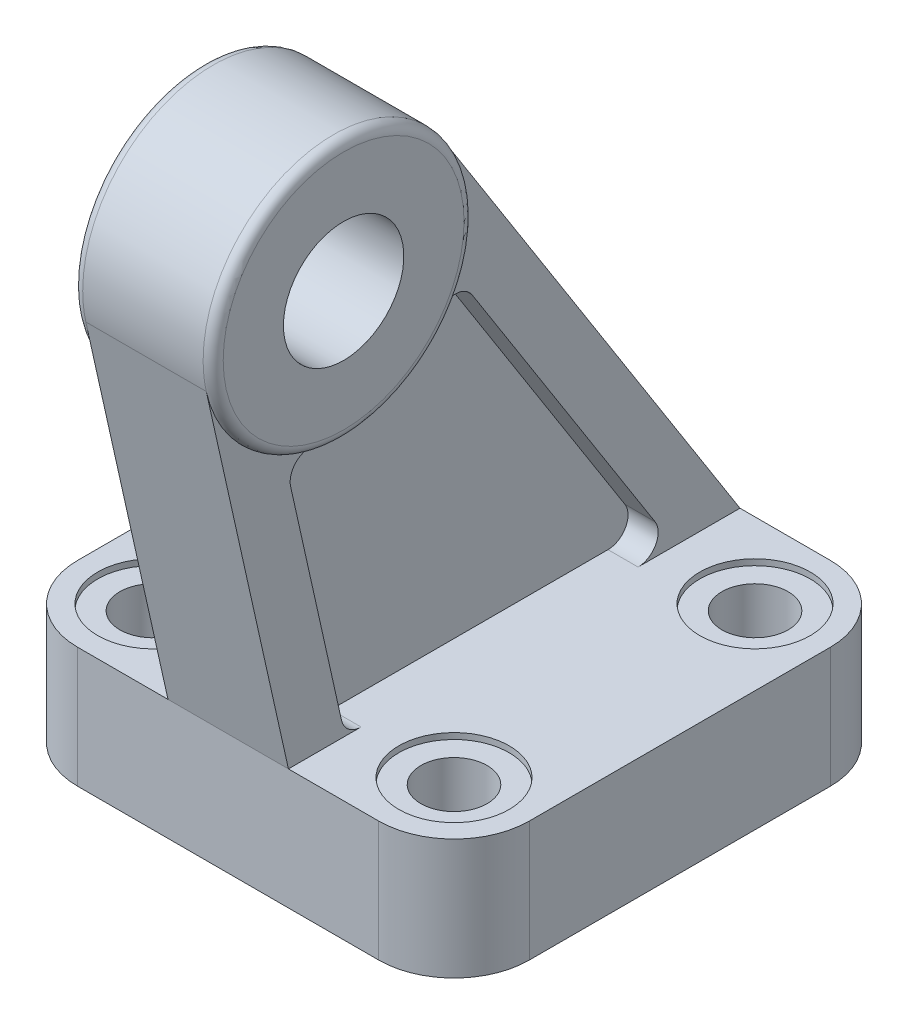
SolidWorks part; units mm, degrees
ref_plane "Front Plane" through (0, 0, 0) normal (0, 0, 1) x (1, 0, 0)
ref_plane "Top Plane" through (0, 0, 0) normal (0, 1, 0) x (1, 0, 0)
ref_plane "Right Plane" through (0, 0, 0) normal (1, 0, 0) x (0, 0, -1)
ref_plane "Plane1" through (0, 0, 0) normal (0, 1, 0) x (1, 0, 0)
sketch "Sketch1" plane through (0, 0, 0) normal (0, 1, 0) x (1, 0, 0)
  line L0 (-15, -22.5) -> (15, -22.5)
  line L1 (22.5, -15) -> (22.5, 15)
  line L2 (15, 22.5) -> (-15, 22.5)
  line L3 (-22.5, 15) -> (-22.5, -15)
  arc A0 (-22.5, -15) -> (-15, -22.5) centre (-15, -15) ccw
  arc A1 (15, -22.5) -> (22.5, -15) centre (15, -15) ccw
  arc A2 (22.5, 15) -> (15, 22.5) centre (15, 15) ccw
  arc A3 (-15, 22.5) -> (-22.5, 15) centre (-15, 15) ccw
  circle A4 centre (15, 15) radius 3.3
  circle A5 centre (15, -15) radius 3.3
  circle A6 centre (-15, 15) radius 3.3
  circle A7 centre (-15, -15) radius 3.3
extrude "Boss-Extrude1" add sketch "Sketch1" along normal blind 12
ref_plane "Plane2" through (0, 0, 0) normal (1, 0, 0) x (0, 0, -1)
sketch "Sketch2" plane through (0, 0, 0) normal (1, 0, 0) x (0, 0, -1)
  line L0 (-30.6875, 48.6669) -> (-22.5, 12)
  line L1 (-22.5, 12) -> (22.5, 12)
  line L2 (22.5, 12) -> (-7.0275, 58.4718)
  arc A0 (-7.0275, 58.4718) -> (-30.6875, 48.6669) centre (-18, 51.5) cw
extrude "Boss-Extrude2" add sketch "Sketch2" against normal blind 6 and the other way blind 6
ref_plane "Plane3" through (6, 0, 0) normal (1, 0, 0) x (0, 0, -1)
sketch "Sketch3" plane through (6, 0, 0) normal (1, 0, 0) x (0, 0, -1)
  line L0 (-22.2785, 36.2457) -> (-17.2138, 13.5641)
  line L1 (-15.2619, 12) -> (12.3433, 12)
  line L2 (14.0314, 15.0726) -> (-4.1857, 43.7434)
  arc A0 (-20.0164, 38.6573) -> (-22.2785, 36.2457) centre (-20.3266, 36.6815) ccw
  arc A1 (-17.2138, 13.5641) -> (-15.2619, 12) centre (-15.2619, 14) ccw
  arc A2 (12.3433, 12) -> (14.0314, 15.0726) centre (12.3433, 14) ccw
  arc A3 (-4.1857, 43.7434) -> (-7.4906, 43.8481) centre (-5.8737, 42.6708) ccw
  arc A4 (-7.4906, 43.8481) -> (-20.0164, 38.6573) centre (-18, 51.5) cw
extrude "Cut-Extrude1" cut sketch "Sketch3" against normal blind 3
ref_plane "Plane4" through (-6, 0, 0) normal (1, 0, 0) x (0, 0, -1)
sketch "Sketch4" plane through (-6, 0, 0) normal (1, 0, 0) x (0, 0, -1)
  line L0 (-22.2785, 36.2457) -> (-17.2138, 13.5641)
  line L1 (-15.2619, 12) -> (12.3433, 12)
  line L2 (14.0314, 15.0726) -> (-4.1857, 43.7434)
  arc A0 (-20.0164, 38.6573) -> (-22.2785, 36.2457) centre (-20.3266, 36.6815) ccw
  arc A1 (-17.2138, 13.5641) -> (-15.2619, 12) centre (-15.2619, 14) ccw
  arc A2 (12.3433, 12) -> (14.0314, 15.0726) centre (12.3433, 14) ccw
  arc A3 (-4.1857, 43.7434) -> (-7.4906, 43.8481) centre (-5.8737, 42.6708) ccw
  arc A4 (-7.4906, 43.8481) -> (-20.0164, 38.6573) centre (-18, 51.5) cw
extrude "Cut-Extrude2" cut sketch "Sketch4" along normal blind 3
ref_plane "Plane5" through (0, 0, 18) normal (0, 0, 1) x (1, 0, 0)
sketch "Sketch5" plane through (0, 0, 18) normal (0, 0, 1) x (1, 0, 0)
  line L0 (-7, 63.5) -> (-7, 57.5)
  line L1 (-7, 57.5) -> (7, 57.5)
  line L2 (7, 57.5) -> (7, 63.5)
  line L3 (6, 64.5) -> (-6, 64.5)
  line L4 (7, 51.5) -> (-7, 51.5) construction
  arc A0 (7, 63.5) -> (6, 64.5) centre (6, 63.5) ccw
  arc A1 (-6, 64.5) -> (-7, 63.5) centre (-6, 63.5) ccw
revolve "Revolve1" add sketch "Sketch5" angle 360 about L4
ref_plane "Plane6" through (0, 0, 0) normal (0, 1, 0) x (1, 0, 0)
sketch "Sketch6" plane through (0, 0, 0) normal (0, 1, 0) x (1, 0, 0)
  line L0 (-17, 6.5) -> (-17, -6.5)
  line L1 (-6.5, -17) -> (6.5, -17)
  line L2 (17, -6.5) -> (17, 6.5)
  line L3 (6.5, 17) -> (-6.5, 17)
  arc A0 (-17, -6.5) -> (-15, -8.5) centre (-15, -6.5) ccw
  arc A1 (-15, -8.5) -> (-8.5, -15) centre (-15, -15) cw
  arc A2 (-8.5, -15) -> (-6.5, -17) centre (-6.5, -15) ccw
  arc A3 (6.5, -17) -> (8.5, -15) centre (6.5, -15) ccw
  arc A4 (8.5, -15) -> (15, -8.5) centre (15, -15) cw
  arc A5 (15, -8.5) -> (17, -6.5) centre (15, -6.5) ccw
  arc A6 (17, 6.5) -> (15, 8.5) centre (15, 6.5) ccw
  arc A7 (15, 8.5) -> (8.5, 15) centre (15, 15) cw
  arc A8 (8.5, 15) -> (6.5, 17) centre (6.5, 15) ccw
  arc A9 (-6.5, 17) -> (-8.5, 15) centre (-6.5, 15) ccw
  arc A10 (-8.5, 15) -> (-15, 8.5) centre (-15, 15) cw
  arc A11 (-15, 8.5) -> (-17, 6.5) centre (-15, 6.5) ccw
extrude "Cut-Extrude3" cut sketch "Sketch6" along normal blind 6
ref_plane "Plane7" through (0, 12, 0) normal (0, 1, 0) x (1, 0, 0)
sketch "Sketch7" plane through (0, 12, 0) normal (0, 1, 0) x (1, 0, 0)
  circle A0 centre (15, 15) radius 5.5
extrude "Cut-Extrude4" cut sketch "Sketch7" against normal blind 0.6
ref_plane "Plane8" through (0, 12, 0) normal (0, 1, 0) x (1, 0, 0)
sketch "Sketch8" plane through (0, 12, 0) normal (0, 1, 0) x (1, 0, 0)
  circle A0 centre (-15, 15) radius 5.5
extrude "Cut-Extrude5" cut sketch "Sketch8" against normal blind 0.6
ref_plane "Plane9" through (0, 12, 0) normal (0, 1, 0) x (1, 0, 0)
sketch "Sketch9" plane through (0, 12, 0) normal (0, 1, 0) x (1, 0, 0)
  circle A0 centre (15, -15) radius 5.5
extrude "Cut-Extrude6" cut sketch "Sketch9" against normal blind 0.6
ref_plane "Plane10" through (0, 12, 0) normal (0, 1, 0) x (1, 0, 0)
sketch "Sketch10" plane through (0, 12, 0) normal (0, 1, 0) x (1, 0, 0)
  circle A0 centre (-15, -15) radius 5.5
extrude "Cut-Extrude7" cut sketch "Sketch10" against normal blind 0.6
